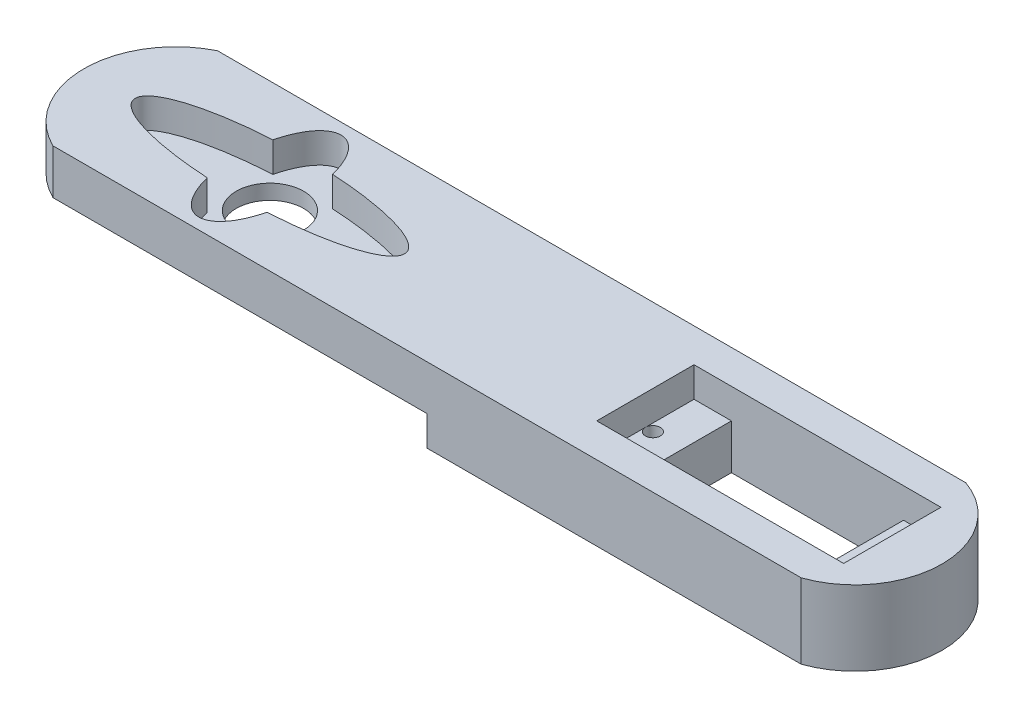
SolidWorks part; units mm, degrees
ref_plane "前视基准面" through (0, 0, 0) normal (0, 0, 1) x (1, 0, 0)
ref_plane "上视基准面" through (0, 0, 0) normal (0, 1, 0) x (1, 0, 0)
ref_plane "右视基准面" through (0, 0, 0) normal (1, 0, 0) x (0, 0, -1)
sketch "草图1" plane through (0, 0, 0) normal (0, 1, 0) x (1, 0, 0)
  line L0 (0, 0) -> (18, 0) construction
  line L5 (0, 0) -> (0, 9.5) construction
  line L6 (66.6765, 0) -> (78.1765, 0) construction
  line L7 (78.1765, 0) -> (78.1765, 6.5)
  line L8 (50.1765, -6.5) -> (83.1765, -6.5)
  line L9 (50.1765, -6.5) -> (50.1765, 6.5)
  line L10 (83.1765, -6.5) -> (83.1765, 6.5)
  line L11 (50.1765, 6.5) -> (83.1765, 6.5)
  line L12 (50.1765, -6.5) -> (83.1765, 6.5) construction
  line L13 (83.1765, -6.5) -> (50.1765, 6.5) construction
  line L14 (78.1765, 0) -> (78.1765, -6.5)
  line L16 (55.1765, 0) -> (55.1765, -6.5)
  line L17 (55.1765, 0) -> (55.1765, 6.5)
  line L18 (-18, 11) -> (82, 11)
  line L19 (0, 0) -> (-4.5, 0)
  line L20 (-18, -11) -> (82, -11)
  line L21 (82, -6.5) -> (82, -6.0365)
  line L22 (82, 6.0365) -> (82, 6.5)
  circle A0 centre (0, 0) radius 4.5
  arc A2 (-18, 11) -> (-18, -11) centre (-12.6022, 0) ccw
  arc A3 (82, 11) -> (82, -11) centre (78.1765, 0) cw
  ellipse E0 centre (0, 0) end of major axis (18, 0) minor radius 4.5 (-3.9912, 4.388) -> (-3.9912, -4.388) ccw
  ellipse E1 centre (0, 0) end of major axis (0, 9.5) minor radius 4.5 (-3.9912, -4.388) -> (3.9912, -4.388) ccw
  ellipse E2 centre (0, 0) end of major axis (0, 9.5) minor radius 4.5 (3.9912, 4.388) -> (-3.9912, 4.388) ccw
  ellipse E3 centre (0, 0) end of major axis (18, 0) minor radius 4.5 (3.9912, -4.388) -> (3.9912, 4.388) ccw
  point P41 (-18, 0)
  dimension "D1" = 33
  dimension "D2" = 13
  dimension "D3" = 11.5
extrude "凸台-拉伸1" add sketch "草图1" along normal mid plane 20 contours A2 L20 A3 L18
ref_plane "基准面1" through (0, 10, 0) normal (0, 1, 0) x (1, 0, 0)
sketch "草图2" plane through (0, 10, 0) normal (0, 1, 0) x (1, 0, 0)
  circle A0 centre (0, 0) radius 4.5
extrude "切除-拉伸1" cut sketch "草图2" against normal through all
sketch "草图3" plane through (0, 10, 0) normal (0, 1, 0) x (1, 0, 0)
  ellipse E0 centre (0, 0) end of major axis (18, 0) minor radius 4.5 (-3.9912, 4.388) -> (-3.9912, -4.388) ccw
  ellipse E1 centre (0, 0) end of major axis (0, 9.5) minor radius 4.5 (-3.9912, -4.388) -> (3.9912, -4.388) ccw
  ellipse E2 centre (0, 0) end of major axis (0, 9.5) minor radius 4.5 (3.9912, 4.388) -> (-3.9912, 4.388) ccw
  ellipse E3 centre (0, 0) end of major axis (18, 0) minor radius 4.5 (3.9912, -4.388) -> (3.9912, 4.388) ccw
extrude "切除-拉伸2" cut sketch "草图3" against normal blind 4
sketch "草图4" plane through (0, 10, 0) normal (0, 1, 0) x (1, 0, 0)
  line L1 (50.1765, -6.5) -> (83.1765, -6.5)
  line L2 (50.1765, -6.5) -> (50.1765, 6.5)
  line L3 (50.1765, 6.5) -> (83.1765, 6.5)
  line L4 (83.1765, -6.5) -> (83.1765, 6.5)
  line L5 (55.1765, -6.5) -> (78.1765, -6.5)
  line L6 (55.1765, -6.5) -> (55.1765, 6.5)
  line L7 (55.1765, 6.5) -> (78.1765, 6.5)
  line L8 (78.1765, -6.5) -> (78.1765, 6.5)
extrude "切除-拉伸3" cut sketch "草图4" against normal through all contours L6 L5 L8 L7
sketch "草图5" plane through (0, 10, 0) normal (0, 1, 0) x (1, 0, 0)
  line L1 (50.1765, -6.5) -> (55.1765, -6.5)
  line L2 (50.1765, -6.5) -> (50.1765, 6.5)
  line L3 (50.1765, 6.5) -> (55.1765, 6.5)
  line L4 (55.1765, -6.5) -> (55.1765, 6.5)
  line L9 (83.1765, -6.5) -> (78.1765, -6.5)
  line L10 (83.1765, -6.5) -> (83.1765, 6.5)
  line L11 (83.1765, 6.5) -> (78.1765, 6.5)
  line L12 (78.1765, -6.5) -> (78.1765, 6.5)
extrude "切除-拉伸4" cut sketch "草图5" against normal blind 4 contours L2 L1 L4 L3 | L10 L9 L12 L11
ref_plane "基准面2" through (0, -10, 0) normal (0, -1, 0) x (-1, 0, 0)
sketch "草图6" plane through (0, -10, 0) normal (0, -1, 0) x (-1, 0, 0)
  line L1 (18, 11) -> (-82, 11)
  line L3 (18, -11) -> (-82, -11)
  arc A0 (18, -11) -> (18, 11) centre (12.6022, 0) ccw
  arc A1 (-82, -11) -> (-82, 11) centre (-78.1765, 0) cw
extrude "切除-拉伸5" cut sketch "草图6" against normal blind 10 contours L1 A1 L3 A0
sketch "草图7" plane through (0, 10, 0) normal (0, 1, 0) x (1, 0, 0)
  circle A0 centre (82.1765, 0) radius 1
  circle A1 centre (51.1765, 0) radius 1
extrude "切除-拉伸6" cut sketch "草图7" against normal through all contours A0 | A1
ref_plane "基准面3" through (0, 0, 0) normal (0, -1, 0) x (-1, 0, 0)
sketch "草图8" plane through (0, 0, 0) normal (0, -1, 0) x (-1, 0, 0)
  line L0 (-32, -11) -> (-32, 11) construction
  line L1 (18, -11) -> (-82, -11) construction
  line L2 (18, 11) -> (-82, 11) construction
  line L3 (-32, -11) -> (18, -11)
  line L4 (-32, 11) -> (18, 11)
  line L5 (-32, -11) -> (-32, 11)
  arc A0 (18, -11) -> (18, 11) centre (12.6022, 0) ccw
extrude "切除-拉伸7" cut sketch "草图8" against normal blind 4 contours L5 L4 A0 L3
